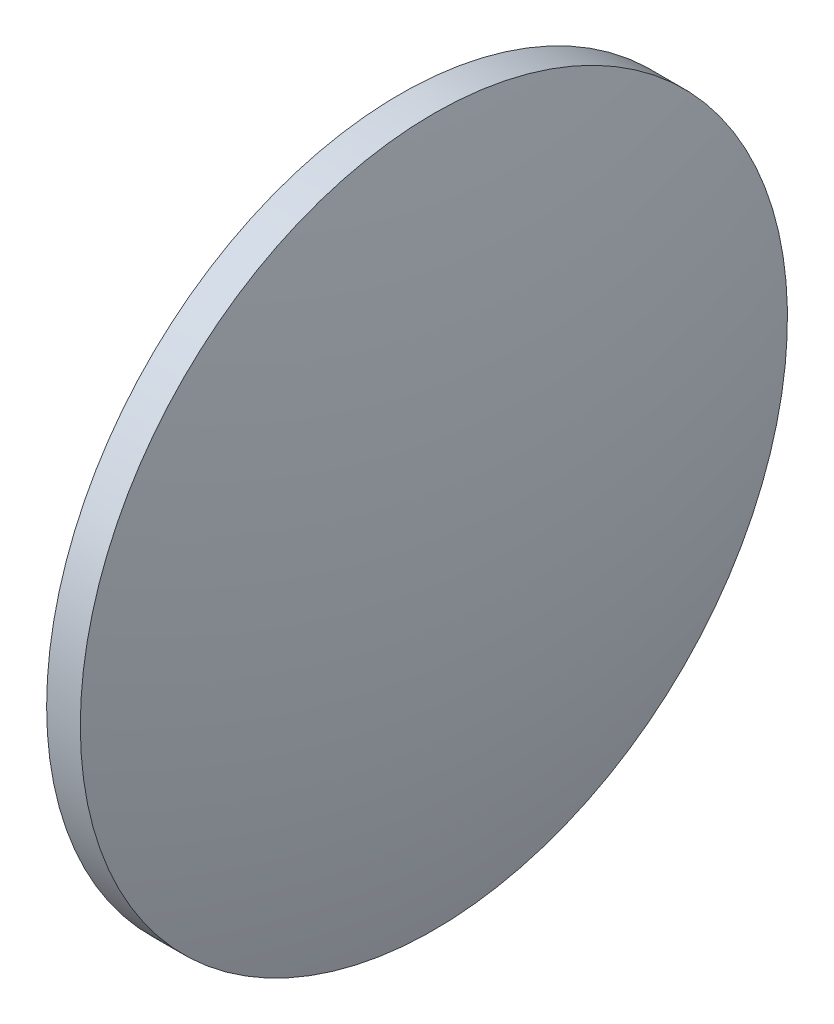
SolidWorks part; units mm, degrees
ref_plane "前视基准面" through (0, 0, 0) normal (0, 0, 1) x (1, 0, 0)
ref_plane "上视基准面" through (0, 0, 0) normal (0, 1, 0) x (1, 0, 0)
ref_plane "右视基准面" through (0, 0, 0) normal (1, 0, 0) x (0, 0, -1)
sketch "草图1" plane through (0, 0, 0) normal (0, 0, 1) x (1, 0, 0)
  line L0 (458.332, 57.8955) -> (502.2842, 57.8955) construction
  line L1 (467.1017, 57.8955) -> (467.1017, 89.3955)
  line L2 (467.1017, 89.3955) -> (470.1017, 89.3955)
  line L3 (474.0017, 57.8955) -> (467.1017, 57.8955)
  arc A0 (474.0017, 57.8955) -> (470.1017, 89.3955) centre (344.8401, 57.8955) ccw
revolve "旋转1" add sketch "草图1" angle 360 about L0
